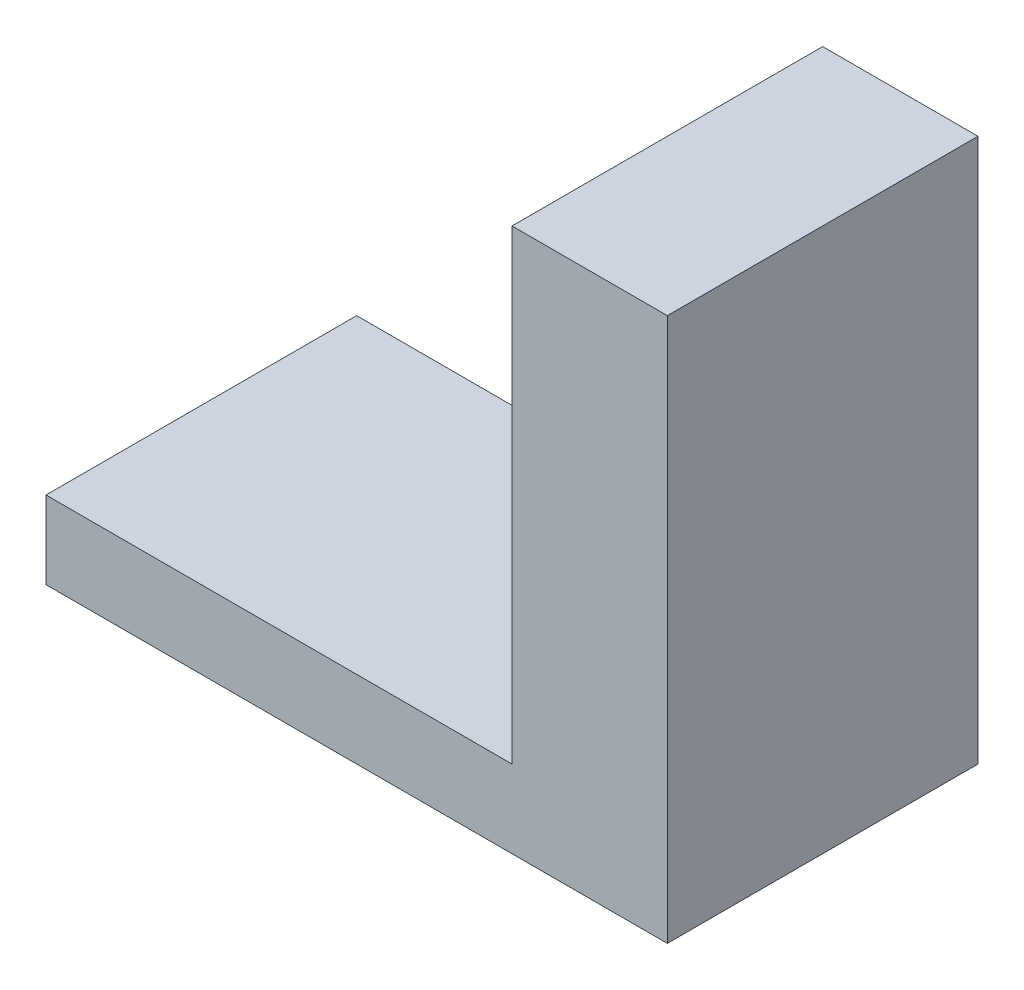
SolidWorks part; units mm, degrees
ref_plane "Front Plane" through (0, 0, 0) normal (0, 0, 1) x (1, 0, 0)
ref_plane "Top Plane" through (0, 0, 0) normal (0, 1, 0) x (1, 0, 0)
ref_plane "Right Plane" through (0, 0, 0) normal (1, 0, 0) x (0, 0, -1)
sketch "Sketch1" plane through (0, 0, 0) normal (0, 1, 0) x (1, 0, 0)
  line L1 (-13.6878, 6.1736) -> (11.7122, 6.1736)
  line L2 (-13.6878, 6.1736) -> (-13.6878, -6.5264)
  line L3 (-13.6878, -6.5264) -> (11.7122, -6.5264)
  line L4 (11.7122, 6.1736) -> (11.7122, -6.5264)
  dimension "D1" = 25.4
  dimension "D2" = 12.7
extrude "Boss-Extrude1" add sketch "Sketch1" along normal blind 3.175
sketch "Sketch2" plane through (0, 3.175, 0) normal (0, 1, 0) x (1, 0, 0)
  line L0 (-13.6878, -6.5264) -> (11.7122, -6.5264) construction
  line L1 (11.7122, 6.1736) -> (5.3622, 6.1736)
  line L2 (11.7122, 6.1736) -> (11.7122, -6.5264)
  line L3 (11.7122, -6.5264) -> (5.3622, -6.5264)
  line L4 (5.3622, 6.1736) -> (5.3622, -6.5264)
  dimension "D1" = 6.35
extrude "Boss-Extrude2" add sketch "Sketch2" along normal blind 19.05
